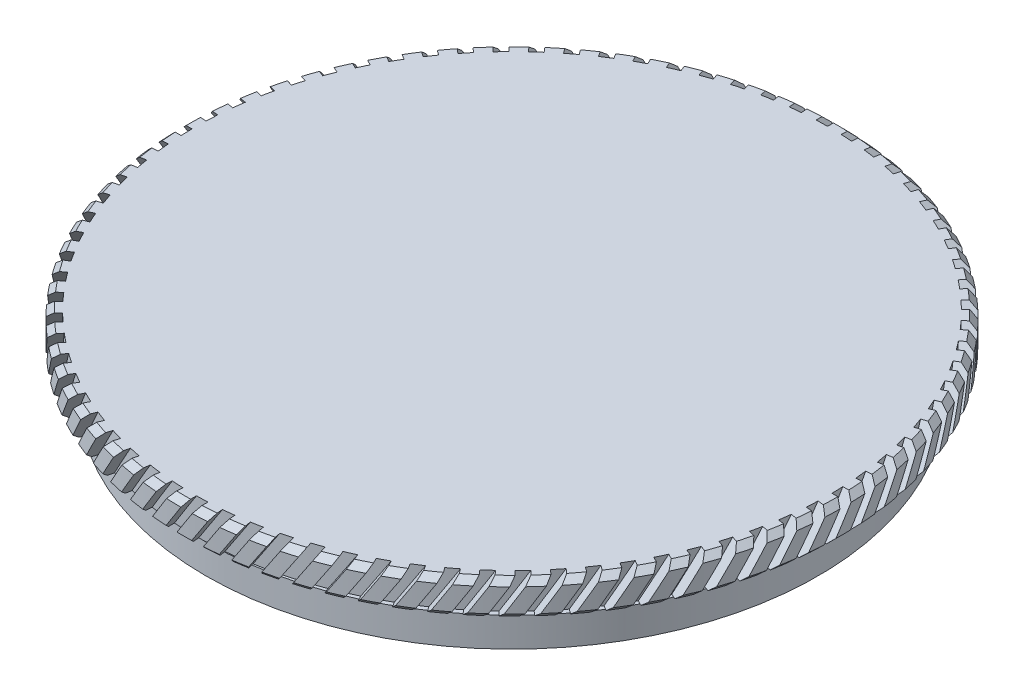
SolidWorks part; units mm, degrees
ref_plane "前视基准面" through (0, 0, 0) normal (0, 0, 1) x (1, 0, 0)
ref_plane "上视基准面" through (0, 0, 0) normal (0, 1, 0) x (1, 0, 0)
ref_plane "右视基准面" through (0, 0, 0) normal (1, 0, 0) x (0, 0, -1)
sketch "草图1" plane through (0, 0, 0) normal (0, 0, 1) x (1, 0, 0)
  line L0 (0, 66.6288) -> (0, -106.6399) construction
  line L1 (-97.6622, 0) -> (93.4292, 0) construction
  line L2 (0, 21.8713) -> (28, 21.8713)
  line L3 (28, 21.8713) -> (28, 18.8713)
  line L4 (25.5, 18.8713) -> (25.5, 17.8713)
  line L5 (25.5, 18.8713) -> (28, 18.8713)
  line L6 (26, 17.8713) -> (26, 15.3713)
  line L7 (25.5, 17.8713) -> (26, 17.8713)
  line L8 (24, 18.8713) -> (24, 15.3713)
  line L9 (0, 21.8713) -> (0, 18.8713)
  line L10 (24, 15.3713) -> (26, 15.3713)
  line L11 (0, 18.8713) -> (24, 18.8713)
  dimension "D1" = 28
  dimension "D2" = 3
  dimension "D3" = 25.5
  dimension "D4" = 26
  dimension "D5" = 24
  dimension "D6" = 1
  dimension "D7" = 2.5
revolve "旋转2" add sketch "草图1" angle 360 about L0
cosmetic thread "装饰螺纹线1" parameters "D2"=51.9999
chamfer "倒角1" distance 0.5 angle 45 2 edges at (0, 21.8713, 28) (0, 18.8713, 28)
sketch "草图2" plane through (0, 0, 0) normal (0, 0, 1) x (1, 0, 0)
  line L0 (1.1082, 23.3033) -> (-5.3395, 13.2735)
  line L1 (1.1082, 23.3033) -> (1.7811, 22.8706)
  line L2 (-5.3395, 13.2735) -> (-4.6666, 12.8409)
  line L3 (1.7811, 22.8706) -> (-4.6666, 12.8409)
  dimension "D1" = 0.8
surface "曲面-等距1" parameters "D1"=1
extrude "切除-拉伸1" cut sketch "草图2" against normal up to surface (13.0228 mm away) from offset 40
delete or keep bodies "实体-删除/保留 1" type delete bodies bodies 107
pattern_circular "阵列(圆周)2" count 80 over 360 about axis through (0, 0, 0) along (0, 1, 0) of "切除-拉伸1"
